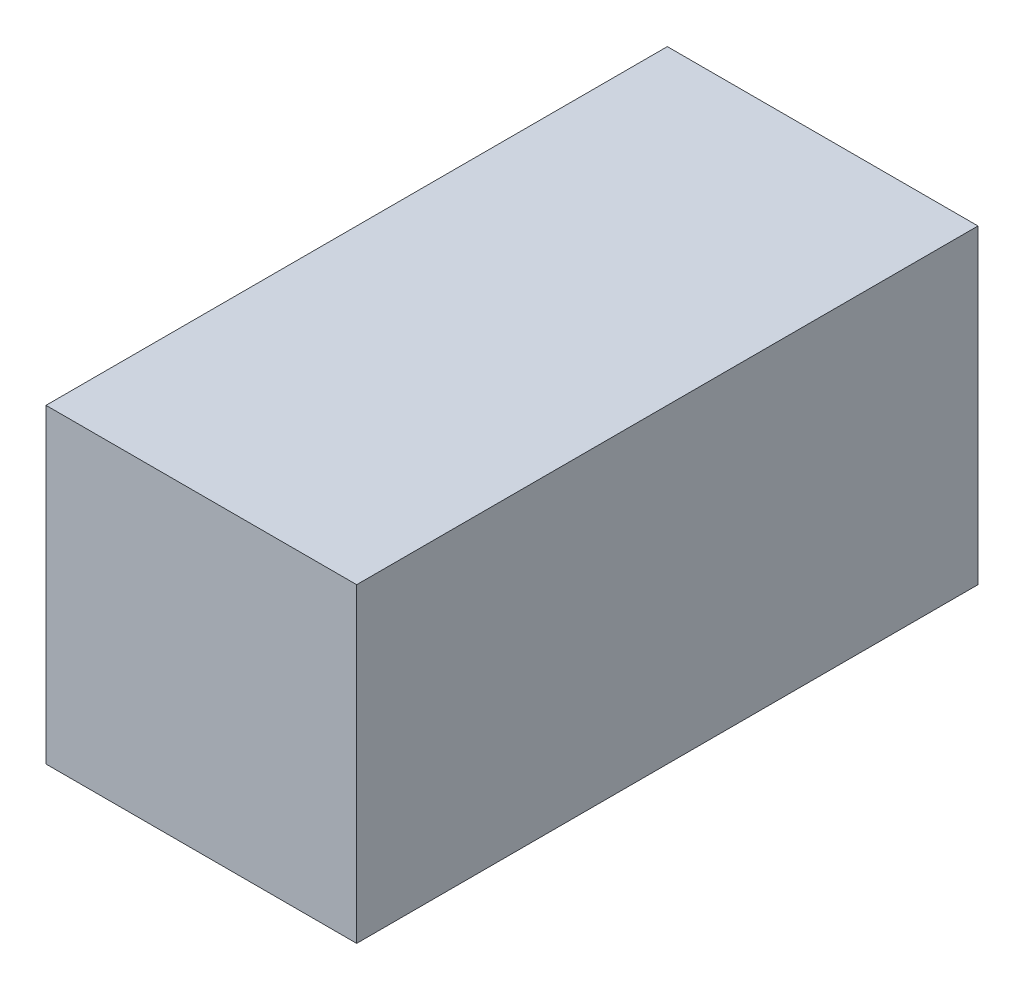
SolidWorks part; units mm, degrees
ref_plane "Front Plane" through (0, 0, 0) normal (0, 0, 1) x (1, 0, 0)
ref_plane "Top Plane" through (0, 0, 0) normal (0, 1, 0) x (1, 0, 0)
ref_plane "Right Plane" through (0, 0, 0) normal (1, 0, 0) x (0, 0, -1)
sketch "Sketch1" plane through (0, 0, 0) normal (0, 0, 1) x (1, 0, 0)
  line L1 (-2, -2) -> (2, -2)
  line L2 (-2, -2) -> (-2, 2)
  line L3 (-2, 2) -> (2, 2)
  line L4 (2, -2) -> (2, 2)
  line L5 (-2, -2) -> (2, 2) construction
  line L6 (-2, 2) -> (2, -2) construction
  point P0 (0, 0)
  dimension "D1" = 4
  dimension "D2" = 4
extrude "Boss-Extrude1" add sketch "Sketch1" along normal blind 8
